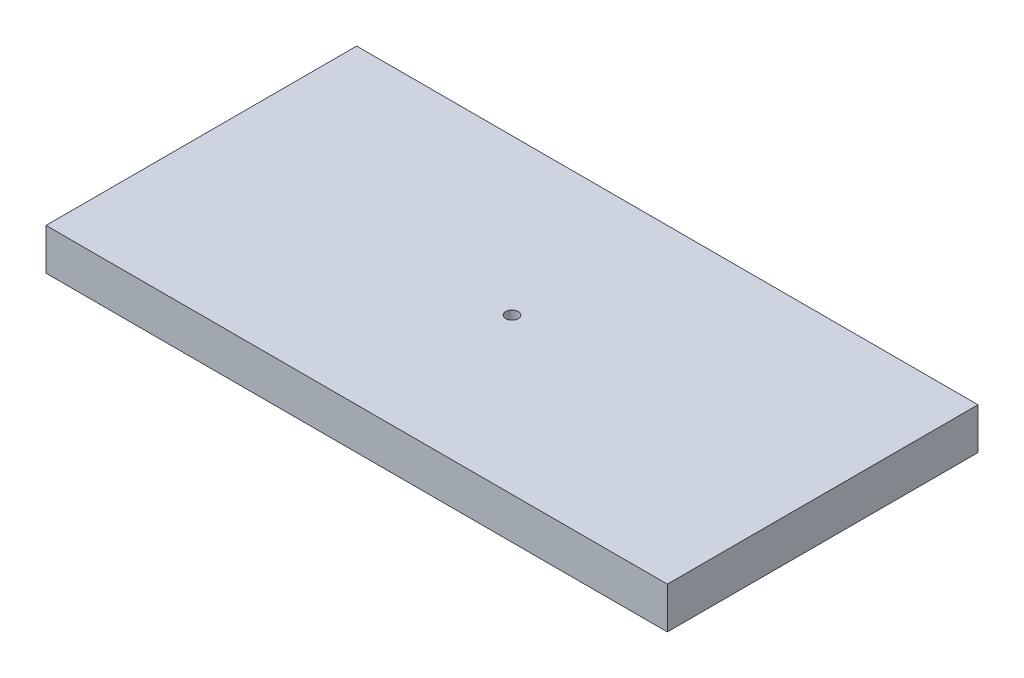
SolidWorks part; units mm, degrees
material "AISI 1020"
ref_plane "Front Plane" through (0, 0, 0) normal (0, 0, 1) x (1, 0, 0)
ref_plane "Top Plane" through (0, 0, 0) normal (0, 1, 0) x (1, 0, 0)
ref_plane "Right Plane" through (0, 0, 0) normal (1, 0, 0) x (0, 0, -1)
sketch "Sketch1" plane through (0, 0, 0) normal (0, 1, 0) x (1, 0, 0)
  line L1 (-150, -75) -> (150, -75)
  line L2 (-150, -75) -> (-150, 75)
  line L3 (-150, 75) -> (150, 75)
  line L4 (150, -75) -> (150, 75)
  line L5 (-150, -75) -> (150, 75) construction
  line L6 (-150, 75) -> (150, -75) construction
  point P0 (0, 0)
  dimension "D1" = 300
  dimension "D2" = 150
extrude "Boss-Extrude1" add sketch "Sketch1" along normal blind 20
sketch "Sketch2" plane through (0, 20, 0) normal (0, 1, 0) x (1, 0, 0)
  circle A0 centre (0, 0) radius 3
  dimension "D1" = 6
extrude "Cut-Extrude1" cut sketch "Sketch2" against normal blind 10
